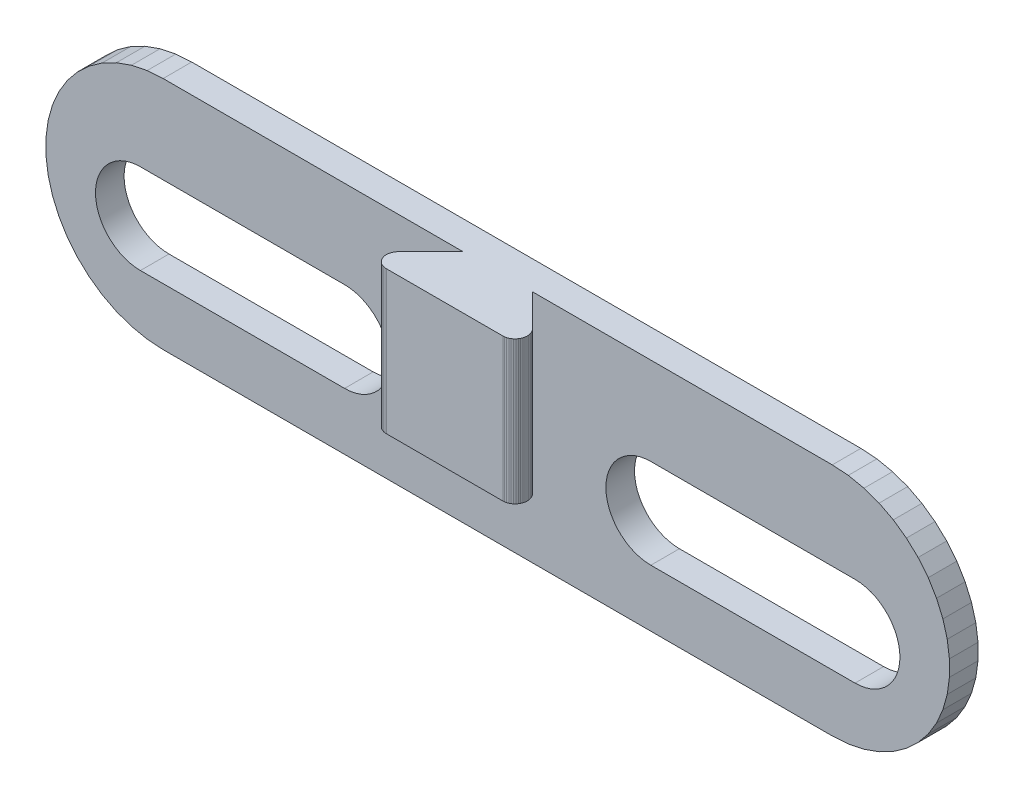
SolidWorks part; units mm, degrees
ref_plane "Front Plane" through (0, 0, 0) normal (0, 0, 1) x (1, 0, 0)
ref_plane "Top Plane" through (0, 0, 0) normal (0, 1, 0) x (1, 0, 0)
ref_plane "Right Plane" through (0, 0, 0) normal (1, 0, 0) x (0, 0, -1)
ref_plane "Plane1" through (0, 0, -1.2) normal (0, 0, 1) x (1, 0, 0)
sketch "Sketch1" plane through (0, 0, -1.2) normal (0, 0, 1) x (1, 0, 0)
  line L0 (17.1705, 2.7464) -> (16.3875, 2.8)
  line L1 (16.3875, 2.8) -> (-16.3875, 2.8)
  line L2 (-16.3875, 2.8) -> (-17.1705, 2.7464)
  line L3 (-17.1705, 2.7464) -> (-17.9388, 2.5867)
  line L4 (-17.9388, 2.5867) -> (-18.6783, 2.3239)
  line L5 (-18.6783, 2.3239) -> (-19.3751, 1.9629)
  line L6 (-19.3751, 1.9629) -> (-20.0163, 1.5103)
  line L7 (-20.0163, 1.5103) -> (-20.5898, 0.9746)
  line L8 (-20.5898, 0.9746) -> (-21.0851, 0.3659)
  line L9 (-21.0851, 0.3659) -> (-21.4929, -0.3047)
  line L10 (-21.4929, -0.3047) -> (-21.8055, -1.0245)
  line L11 (-21.8055, -1.0245) -> (-22.0172, -1.7802)
  line L12 (-22.0172, -1.7802) -> (-22.1241, -2.5577)
  line L13 (-22.1241, -2.5577) -> (-22.1241, -3.3424)
  line L14 (-22.1241, -3.3424) -> (-22.0172, -4.1199)
  line L15 (-22.0172, -4.1199) -> (-21.8055, -4.8756)
  line L16 (-21.8055, -4.8756) -> (-21.4929, -5.5954)
  line L17 (-21.4929, -5.5954) -> (-21.0851, -6.266)
  line L18 (-21.0851, -6.266) -> (-20.5898, -6.8747)
  line L19 (-20.5898, -6.8747) -> (-20.0163, -7.4104)
  line L20 (-20.0163, -7.4104) -> (-19.3751, -7.863)
  line L21 (-19.3751, -7.863) -> (-18.6783, -8.224)
  line L22 (-18.6783, -8.224) -> (-17.9388, -8.4868)
  line L23 (-17.9388, -8.4868) -> (-17.1705, -8.6465)
  line L24 (-17.1705, -8.6465) -> (-16.3875, -8.7001)
  line L25 (-16.3875, -8.7001) -> (16.3875, -8.7001)
  line L26 (16.3875, -8.7001) -> (17.1705, -8.6465)
  line L27 (17.1705, -8.6465) -> (17.9388, -8.4868)
  line L28 (17.9388, -8.4868) -> (18.6783, -8.224)
  line L29 (18.6783, -8.224) -> (19.3751, -7.863)
  line L30 (19.3751, -7.863) -> (20.0163, -7.4104)
  line L31 (20.0163, -7.4104) -> (20.5898, -6.8747)
  line L32 (20.5898, -6.8747) -> (21.0851, -6.266)
  line L33 (21.0851, -6.266) -> (21.4929, -5.5954)
  line L34 (21.4929, -5.5954) -> (21.8055, -4.8756)
  line L35 (21.8055, -4.8756) -> (22.0172, -4.1199)
  line L36 (22.0172, -4.1199) -> (22.1241, -3.3424)
  line L37 (22.1241, -3.3424) -> (22.1241, -2.5577)
  line L38 (22.1241, -2.5577) -> (22.0172, -1.7802)
  line L39 (22.0172, -1.7802) -> (21.8055, -1.0245)
  line L40 (21.8055, -1.0245) -> (21.4929, -0.3047)
  line L41 (21.4929, -0.3047) -> (21.0851, 0.3659)
  line L42 (21.0851, 0.3659) -> (20.5898, 0.9746)
  line L43 (20.5898, 0.9746) -> (20.0163, 1.5103)
  line L44 (20.0163, 1.5103) -> (19.3751, 1.9629)
  line L45 (19.3751, 1.9629) -> (18.6783, 2.3239)
  line L46 (18.6783, 2.3239) -> (17.9388, 2.5867)
  line L47 (17.9388, 2.5867) -> (17.1705, 2.7464)
extrude "Boss-Extrude1" add sketch "Sketch1" against normal blind 1.4
sketch "Sketch2" plane through (0, 0, -1.2) normal (0, 0, 1) x (1, 0, 0)
  line L0 (-17.5, -5.9001) -> (-17.5, -1.5001) construction
  line L2 (-7.5, -5.9001) -> (-17.5, -5.9001)
  line L3 (-16.3875, -8.7001) -> (16.3875, -8.7001) construction
  line L33 (-7.5, -1.5001) -> (-17.5, -1.5001)
  arc A0 (-17.5, -1.5001) -> (-17.5, -5.9001) centre (-17.5, -3.7001) ccw
  arc A1 (-7.5, -1.5001) -> (-7.5, -5.9001) centre (-7.5, -3.7001) cw
  dimension "D1" = 4.4
  dimension "D2" = 2.8
  dimension "D3" = 10
extrude "Cut-Extrude1" cut sketch "Sketch2" against normal through all
sketch "Sketch5" plane through (0, 0, -1.2) normal (0, 0, 1) x (1, 0, 0)
  line L0 (0, -8.7001) -> (0, 2.8) construction
  line L1 (-16.3875, -8.7001) -> (16.3875, -8.7001) construction
  line L2 (16.3875, 2.8) -> (-16.3875, 2.8) construction
sketch "Sketch3" plane through (0, 0, -2.6) normal (0, 0, -1) x (-1, 0, 0)
  line L0 (-18.7424, -5.3604) -> (-18.5729, -5.5188)
  line L1 (-18.5729, -5.5188) -> (-18.3833, -5.6526)
  line L2 (-18.3833, -5.6526) -> (-18.1773, -5.7593)
  line L3 (-18.1773, -5.7593) -> (-17.9587, -5.837)
  line L4 (-17.9587, -5.837) -> (-17.7315, -5.8842)
  line L5 (-17.7315, -5.8842) -> (-17.5, -5.9001)
  line L6 (-17.5, -5.9001) -> (-7.5, -5.9001)
  line L7 (-7.5, -5.9001) -> (-7.2685, -5.8842)
  line L8 (-7.2685, -5.8842) -> (-7.0413, -5.837)
  line L9 (-7.0413, -5.837) -> (-6.8227, -5.7593)
  line L10 (-6.8227, -5.7593) -> (-6.6167, -5.6526)
  line L11 (-6.6167, -5.6526) -> (-6.4272, -5.5188)
  line L12 (-6.4272, -5.5188) -> (-6.2576, -5.3604)
  line L13 (-6.2576, -5.3604) -> (-6.1112, -5.1804)
  line L14 (-6.1112, -5.1804) -> (-5.9906, -4.9822)
  line L15 (-5.9906, -4.9822) -> (-5.8982, -4.7693)
  line L16 (-5.8982, -4.7693) -> (-5.8356, -4.5459)
  line L17 (-5.8356, -4.5459) -> (-5.804, -4.3161)
  line L18 (-5.804, -4.3161) -> (-5.804, -4.084)
  line L19 (-5.804, -4.084) -> (-5.8356, -3.8542)
  line L20 (-5.8356, -3.8542) -> (-5.8982, -3.6308)
  line L21 (-5.8982, -3.6308) -> (-5.9906, -3.4179)
  line L22 (-5.9906, -3.4179) -> (-6.1112, -3.2197)
  line L23 (-6.1112, -3.2197) -> (-6.2576, -3.0397)
  line L24 (-6.2576, -3.0397) -> (-6.4272, -2.8813)
  line L25 (-6.4272, -2.8813) -> (-6.6167, -2.7475)
  line L26 (-6.6167, -2.7475) -> (-6.8227, -2.6408)
  line L27 (-6.8227, -2.6408) -> (-7.0413, -2.5631)
  line L28 (-7.0413, -2.5631) -> (-7.2685, -2.5159)
  line L29 (-7.2685, -2.5159) -> (-7.5, -2.5001)
  line L30 (-7.5, -2.5001) -> (-17.5, -2.5001)
  line L31 (-17.5, -2.5001) -> (-17.7315, -2.5159)
  line L32 (-17.7315, -2.5159) -> (-17.9587, -2.5631)
  line L33 (-17.9587, -2.5631) -> (-18.1773, -2.6408)
  line L34 (-18.1773, -2.6408) -> (-18.3833, -2.7475)
  line L35 (-18.3833, -2.7475) -> (-18.5729, -2.8813)
  line L36 (-18.5729, -2.8813) -> (-18.7424, -3.0397)
  line L37 (-18.7424, -3.0397) -> (-18.8888, -3.2197)
  line L38 (-18.8888, -3.2197) -> (-19.0094, -3.4179)
  line L39 (-19.0094, -3.4179) -> (-19.1018, -3.6308)
  line L40 (-19.1018, -3.6308) -> (-19.1644, -3.8542)
  line L41 (-19.1644, -3.8542) -> (-19.196, -4.084)
  line L42 (-19.196, -4.084) -> (-19.196, -4.3161)
  line L43 (-19.196, -4.3161) -> (-19.1644, -4.5459)
  line L44 (-19.1644, -4.5459) -> (-19.1018, -4.7693)
  line L45 (-19.1018, -4.7693) -> (-19.0094, -4.9822)
  line L46 (-19.0094, -4.9822) -> (-18.8888, -5.1804)
  line L47 (-18.8888, -5.1804) -> (-18.7424, -5.3604)
ref_plane "Plane3" through (0, 0, 0) normal (1, 0, 0) x (0, 1, 0)
mirror "Mirror1" about plane through (0, 0, 0) normal (1, 0, 0) of "Cut-Extrude1"
ref_plane "Plane2" through (0, 2.8, 0) normal (0, 1, 0) x (1, 0, 0)
sketch "Sketch4" plane through (0, 2.8, 0) normal (0, 1, 0) x (1, 0, 0)
  line L0 (3.3303, -0.4384) -> (3.2757, -0.3757)
  line L1 (3.2757, -0.3757) -> (1.7, 1.2)
  line L2 (1.7, 1.2) -> (-1.7, 1.2)
  line L3 (-1.7, 1.2) -> (-3.2757, -0.3757)
  line L4 (-3.2757, -0.3757) -> (-3.3303, -0.4384)
  line L5 (-3.3303, -0.4384) -> (-3.3756, -0.508)
  line L6 (-3.3756, -0.508) -> (-3.411, -0.5833)
  line L7 (-3.411, -0.5833) -> (-3.4355, -0.6626)
  line L8 (-3.4355, -0.6626) -> (-3.4489, -0.7446)
  line L9 (-3.4489, -0.7446) -> (-3.4508, -0.8277)
  line L10 (-3.4508, -0.8277) -> (-3.4413, -0.9102)
  line L11 (-3.4413, -0.9102) -> (-3.4204, -0.9907)
  line L12 (-3.4204, -0.9907) -> (-3.3886, -1.0674)
  line L13 (-3.3886, -1.0674) -> (-3.3465, -1.1391)
  line L14 (-3.3465, -1.1391) -> (-3.2949, -1.2042)
  line L15 (-3.2949, -1.2042) -> (-3.2348, -1.2616)
  line L16 (-3.2348, -1.2616) -> (-3.1673, -1.3101)
  line L17 (-3.1673, -1.3101) -> (-3.0938, -1.3489)
  line L18 (-3.0938, -1.3489) -> (-3.0157, -1.3771)
  line L19 (-3.0157, -1.3771) -> (-2.9344, -1.3942)
  line L20 (-2.9344, -1.3942) -> (-2.8515, -1.4)
  line L21 (-2.8515, -1.4) -> (2.8515, -1.4)
  line L22 (2.8515, -1.4) -> (2.9344, -1.3942)
  line L23 (2.9344, -1.3942) -> (3.0157, -1.3771)
  line L24 (3.0157, -1.3771) -> (3.0938, -1.3489)
  line L25 (3.0938, -1.3489) -> (3.1673, -1.3101)
  line L26 (3.1673, -1.3101) -> (3.2348, -1.2616)
  line L27 (3.2348, -1.2616) -> (3.2949, -1.2042)
  line L28 (3.2949, -1.2042) -> (3.3465, -1.1391)
  line L29 (3.3465, -1.1391) -> (3.3886, -1.0674)
  line L30 (3.3886, -1.0674) -> (3.4204, -0.9907)
  line L31 (3.4204, -0.9907) -> (3.4413, -0.9102)
  line L32 (3.4413, -0.9102) -> (3.4508, -0.8277)
  line L33 (3.4508, -0.8277) -> (3.4489, -0.7446)
  line L34 (3.4489, -0.7446) -> (3.4355, -0.6626)
  line L35 (3.4355, -0.6626) -> (3.411, -0.5833)
  line L36 (3.411, -0.5833) -> (3.3756, -0.508)
  line L37 (3.3756, -0.508) -> (3.3303, -0.4384)
extrude "Boss-Extrude2" add sketch "Sketch4" against normal blind 7
